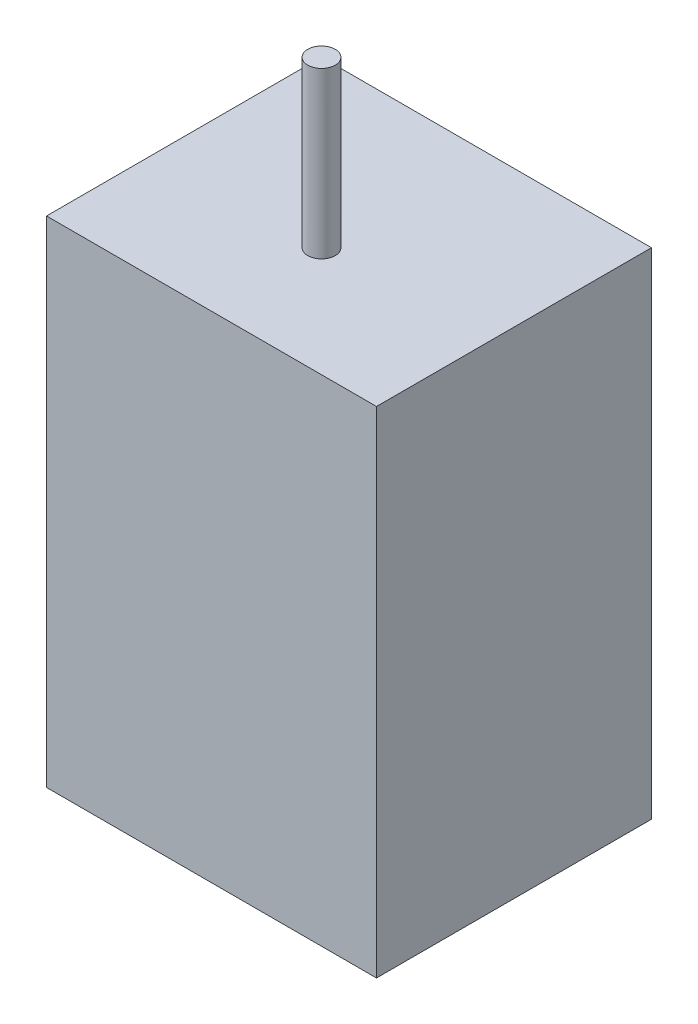
SolidWorks part; units mm, degrees
ref_plane "Front Plane" through (0, 0, 0) normal (0, 0, 1) x (1, 0, 0)
ref_plane "Top Plane" through (0, 0, 0) normal (0, 1, 0) x (1, 0, 0)
ref_plane "Right Plane" through (0, 0, 0) normal (1, 0, 0) x (0, 0, -1)
sketch "Sketch1" plane through (0, 0, 0) normal (0, 1, 0) x (1, 0, 0)
  line L1 (0, 0) -> (19.05, 0)
  line L2 (0, 0) -> (0, 15.875)
  line L3 (0, 15.875) -> (19.05, 15.875)
  line L4 (19.05, 0) -> (19.05, 15.875)
  dimension "D1" = 19.05
  dimension "D2" = 15.875
extrude "Boss-Extrude1" add sketch "Sketch1" along normal blind 28.575
sketch "Sketch2" plane through (0, 28.575, 0) normal (0, 1, 0) x (1, 0, 0)
  line L0 (0, 0) -> (19.05, 0) construction
  line L1 (0, 6.35) -> (19.05, 6.35)
  line L2 (0, 15.875) -> (0, 0) construction
  line L3 (19.05, 0) -> (19.05, 15.875) construction
  line L4 (9.525, 15.875) -> (9.525, 0) construction
  line L5 (19.05, 15.875) -> (0, 15.875) construction
  circle A0 centre (9.525, 6.35) radius 0.7937
  dimension "D2" = 1.5875
  dimension "D1" = 6.35
extrude "Boss-Extrude2" add sketch "Sketch2" along normal blind 9.525 contours L1 A0 | L1 A0
